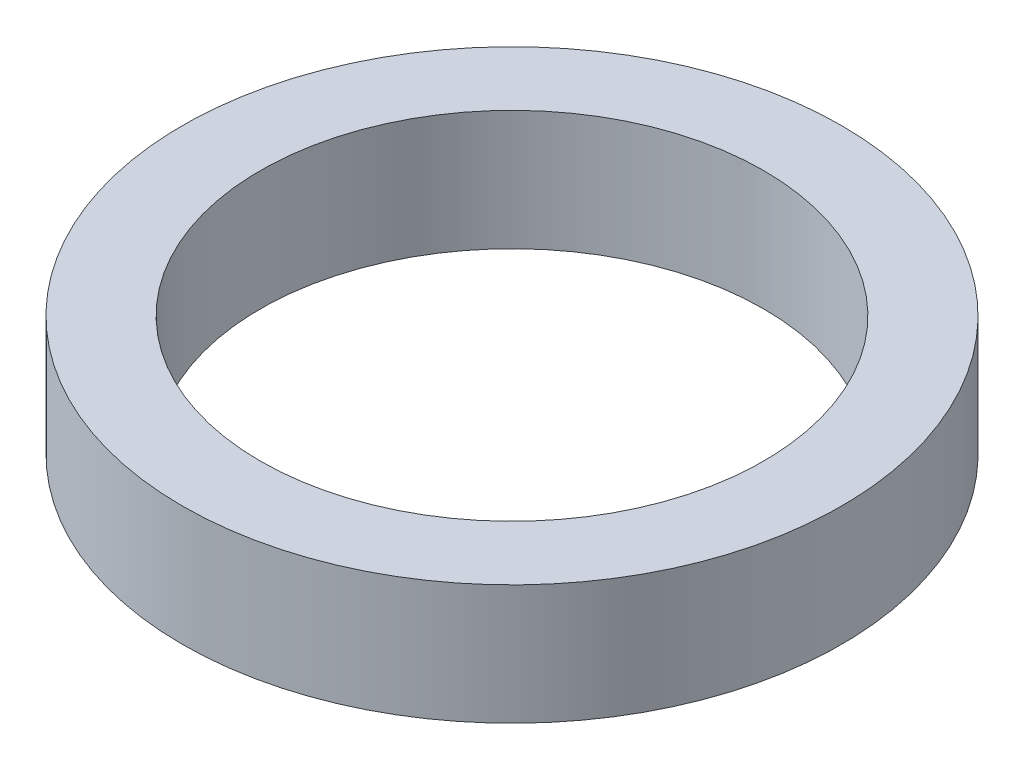
SolidWorks part; units mm, degrees
ref_plane "Front Plane" through (0, 0, 0) normal (0, 0, 1) x (1, 0, 0)
ref_plane "Top Plane" through (0, 0, 0) normal (0, 1, 0) x (1, 0, 0)
ref_plane "Right Plane" through (0, 0, 0) normal (1, 0, 0) x (0, 0, -1)
sketch "Sketch1" plane through (0, 0, 0) normal (0, 1, 0) x (1, 0, 0)
  circle A0 centre (0, 0) radius 5.5
  circle A1 centre (0, 0) radius 4.2
  dimension "D1" = 11
  dimension "D2" = 8.4
extrude "Boss-Extrude1" add sketch "Sketch1" along normal blind 2
equation "\"D1\"= 11 - 2.50mm"
